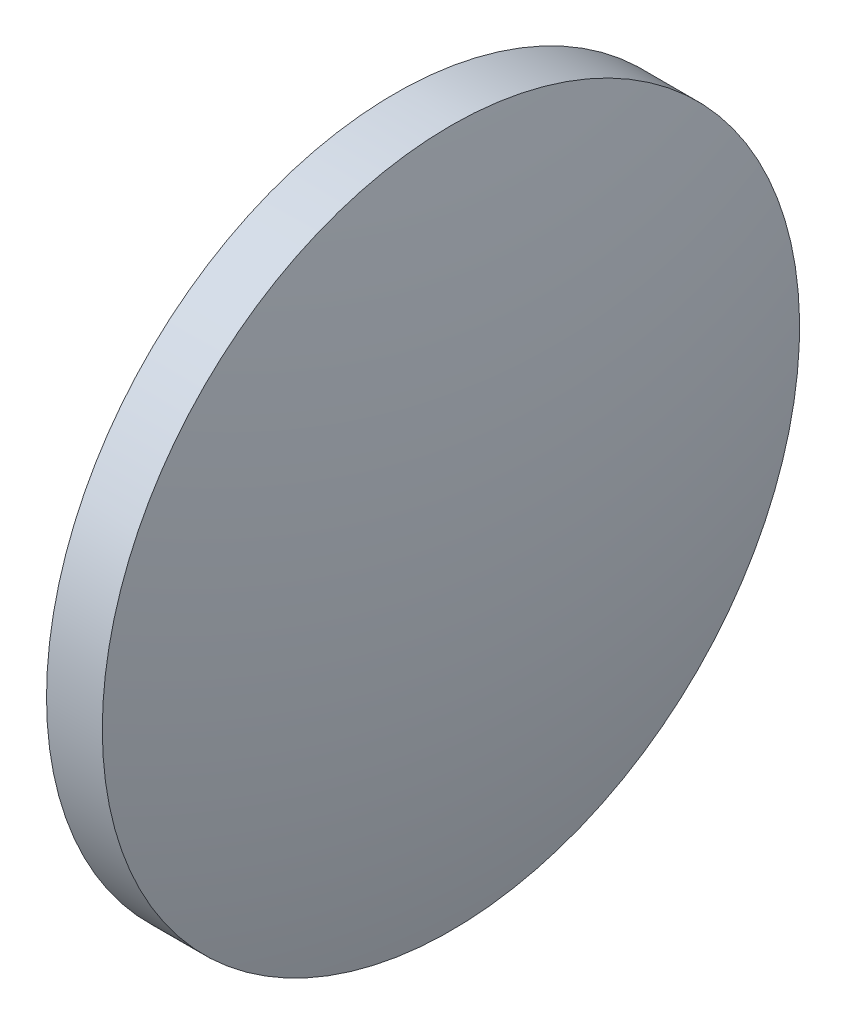
SolidWorks part; units mm, degrees
ref_plane "前视基准面" through (0, 0, 0) normal (0, 0, 1) x (1, 0, 0)
ref_plane "上视基准面" through (0, 0, 0) normal (0, 1, 0) x (1, 0, 0)
ref_plane "右视基准面" through (0, 0, 0) normal (1, 0, 0) x (0, 0, -1)
sketch "草图1" plane through (0, 0, 0) normal (0, 0, 1) x (1, 0, 0)
  line L0 (54.3328, 32.5105) -> (63.9209, 32.5105) construction
  line L1 (56.6984, 32.5105) -> (56.6984, 45.0105)
  line L2 (60.2384, 32.5105) -> (56.6984, 32.5105)
  line L5 (56.6984, 45.0105) -> (58.6984, 45.0105)
  arc A0 (60.2384, 32.5105) -> (58.6984, 45.0105) centre (8.7379, 32.5105) ccw
revolve "旋转1" add sketch "草图1" angle 360 about L0
